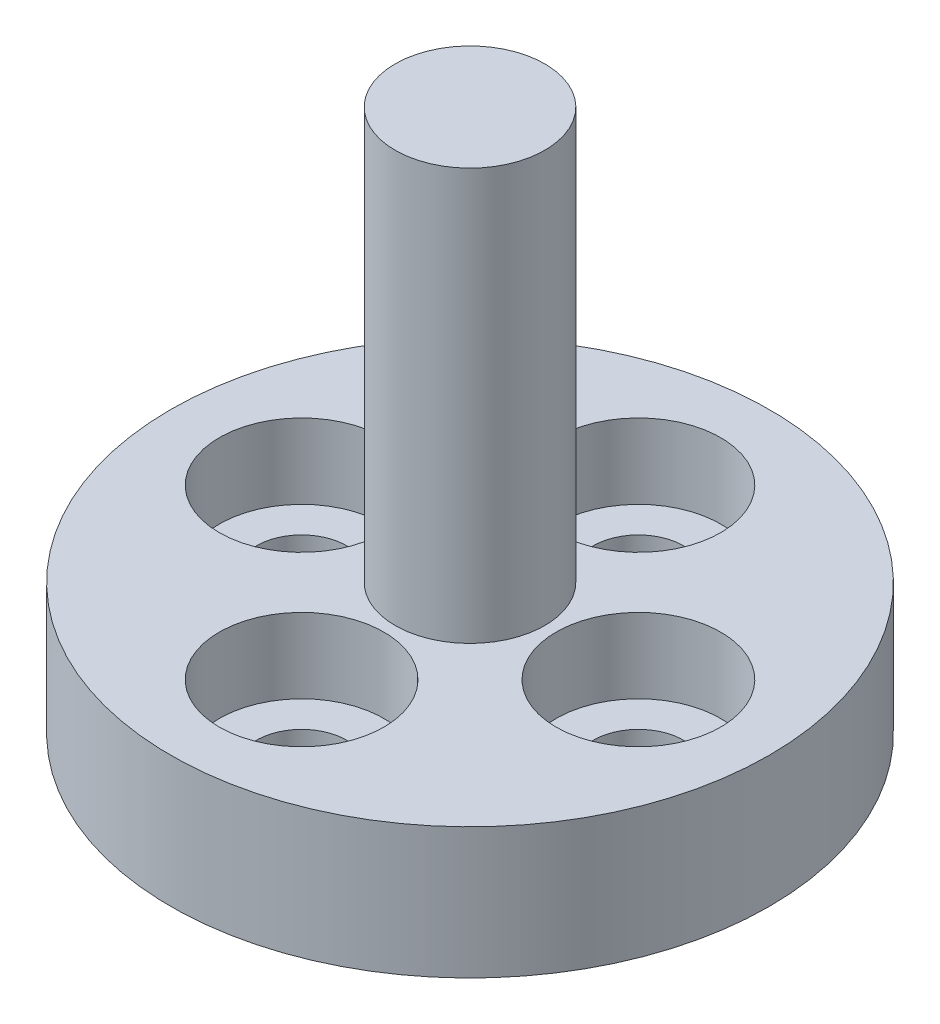
SolidWorks part; units mm, degrees
ref_plane "Front Plane" through (0, 0, 0) normal (0, 0, 1) x (1, 0, 0)
ref_plane "Top Plane" through (0, 0, 0) normal (0, 1, 0) x (1, 0, 0)
ref_plane "Right Plane" through (0, 0, 0) normal (1, 0, 0) x (0, 0, -1)
sketch "Sketch3" plane through (0, 0, 0) normal (0, 0, 1) x (1, 0, 0)
  line L0 (0, 0) -> (8, 0)
  line L1 (8, 0) -> (8, 3.5)
  line L2 (8, 3.5) -> (2, 3.5)
  line L3 (2, 3.5) -> (2, 14.5)
  line L4 (2, 14.5) -> (0, 14.5)
  line L5 (0, 14.5) -> (0, 0)
  dimension "D1" = 8
  dimension "D2" = 14.5
  dimension "D3" = 2
  dimension "D4" = 11
revolve "Revolve1" add sketch "Sketch3" angle 360 about L5
sketch "Sketch4" plane through (0, 3.5, 0) normal (0, 1, 0) x (1, 0, 0)
  circle A0 centre (0, 0) radius 4.5
  dimension "D1" = 9
hole_wizard "CBORE for M2 SHCS2" positions "Sketch8" profile "Sketch7" counterbore size "M2" standard "ANSI Metric" end condition through all
sketch "Sketch8" plane through (0, 3.5, 0) normal (0, 1, 0) x (1, 0, 0)
  circle A0 centre (0, 0) radius 4.5 construction
  point P1 (4.5, 0)
  point P5 (0, -4.5)
  point P7 (0, 4.5)
  point P9 (-4.5, 0)
sketch "Sketch7" plane through (4.5, 3.5, 0) normal (1, 0, 0) x (0, 0, 1)
  line L0 (0, 0) -> (0, 3.5)
  line L1 (0, 3.5) -> (1.2, 3.5)
  line L3 (1.2, 3.5) -> (1.2, 2)
  line L4 (1.2, 2) -> (2.2, 2)
  line L5 (2.2, 2) -> (2.2, 0)
  line L7 (2.2, 0) -> (0, 0)
  line L11 (0, -6.35) -> (0, 107.95) construction
  dimension "Thru Hole Dia." = 2.4
  dimension "Thru Hole Depth" = 3.5
  dimension "C'Bore Dia." = 4.4
  dimension "C'Bore Depth" = 2
